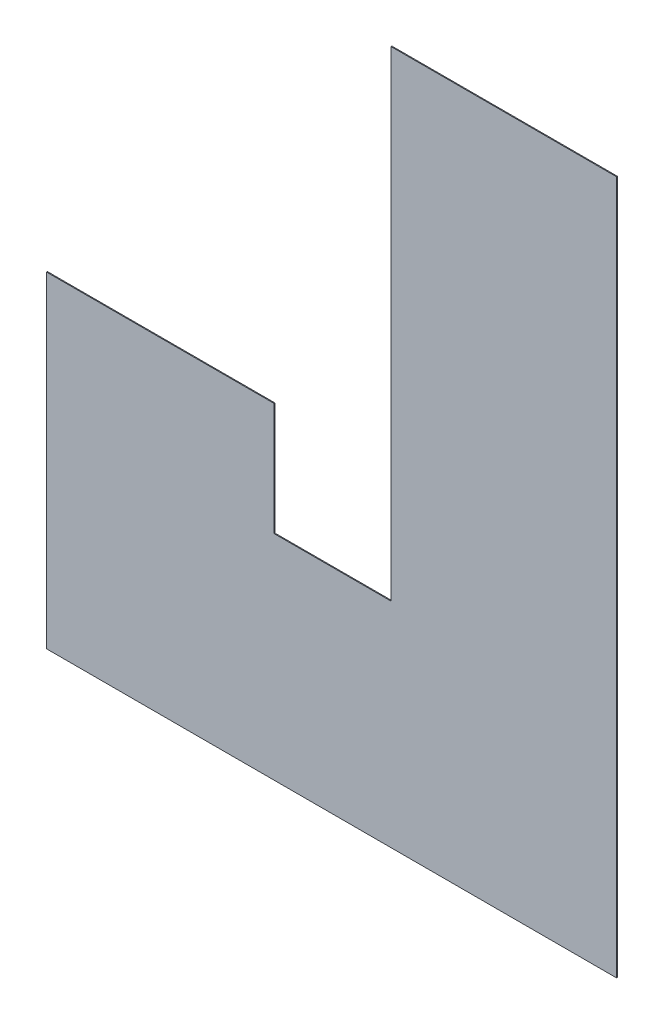
SolidWorks part; units mm, degrees
ref_plane "Plano frontal" through (0, 0, 0) normal (0, 0, 1) x (1, 0, 0)
ref_plane "Plano superior" through (0, 0, 0) normal (0, 1, 0) x (1, 0, 0)
ref_plane "Plano direito" through (0, 0, 0) normal (1, 0, 0) x (0, 0, -1)
sketch "Sketch1" plane through (0, 0, 40625.2208) normal (0, 0, 1) x (1, 0, 0)
  line L0 (-14521.6177, -20082.5186) -> (-42361.227, -20082.5186) construction
  line L1 (-7996.6177, 3307.4814) -> (-15606.6177, 3307.4814)
  line L2 (-7996.6177, 3307.4814) -> (-7996.6177, -20082.5186)
  line L3 (-7996.6177, -20082.5186) -> (-15606.6177, -20082.5186)
  line L4 (-15606.6177, 3307.4814) -> (-15606.6177, -20082.5186)
  line L6 (-15606.6177, -20082.5186) -> (-27221.6177, -20082.5186)
  line L7 (-15606.6177, -20082.5186) -> (-15606.6177, -12882.5186)
  line L8 (-15606.6177, -12882.5186) -> (-27221.6177, -12882.5186)
  line L9 (-27221.6177, -20082.5186) -> (-27221.6177, -12882.5186)
  line L10 (-27221.6177, -17042.5186) -> (-27221.6177, -9082.5186) construction
  line L12 (-27221.6177, -12882.5186) -> (-19546.6177, -12882.5186)
  line L13 (-27221.6177, -12882.5186) -> (-27221.6177, -9082.5186)
  line L14 (-27221.6177, -9082.5186) -> (-19546.6177, -9082.5186)
  line L15 (-19546.6177, -12882.5186) -> (-19546.6177, -9082.5186)
  point P8 (0, 0)
  line M3 (-19546.6177, -9107.5186) -> (-19546.6177, -12882.5186)
  line M4 (-19546.6177, -12882.5186) -> (-16246.6177, -12882.5186)
extrude "Boss-Extrude1" add sketch "Sketch1" along normal blind 30 contours L1 L4 L3 L2 | L9 L6 L4 L8 M4 | L15 L14 L13 L8 M3
